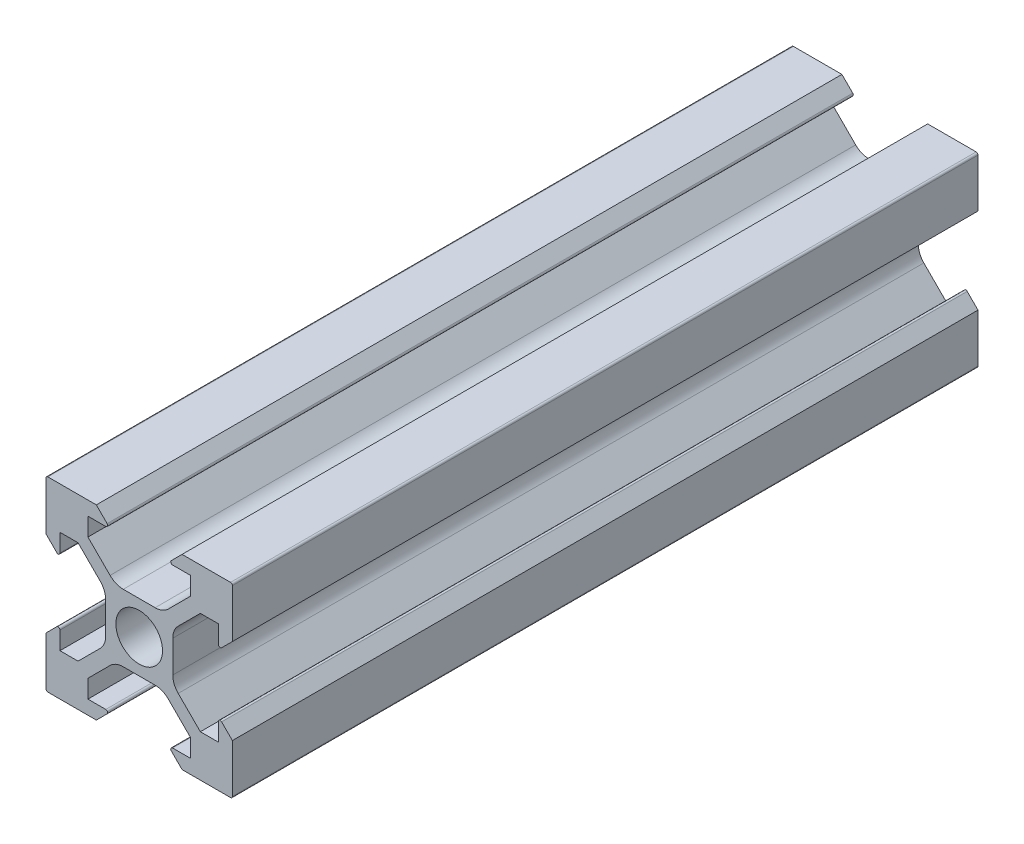
SolidWorks part; units mm, degrees
material "Liga 1350"
ref_plane "Plano frontal" through (0, 0, 0) normal (0, 0, 1) x (1, 0, 0)
ref_plane "Plano superior" through (0, 0, 0) normal (0, 1, 0) x (1, 0, 0)
ref_plane "Plano direito" through (0, 0, 0) normal (1, 0, 0) x (0, 0, -1)
sketch "Esboço1" plane through (0, 0, 0) normal (0, 0, 1) x (1, 0, 0)
  line L0 (0, 13.8681) -> (0, -15.879) construction
  line L1 (-4.6, -10) -> (-9.8, -10)
  line L2 (-3.4414, -8.8414) -> (-4.6, -10)
  line L3 (-4.1858, -3.1251) -> (-6.5607, -5.5)
  line L4 (-10, 9.8) -> (-10, 4.6)
  line L5 (-5.5, -8.5) -> (-3.5828, -8.5)
  line L6 (-5.5, -8.5) -> (-5.5, -6.5607)
  line L7 (-8.5, -5.5) -> (-8.5, -3.5828)
  line L8 (-21.5514, 0) -> (2.5, 0) construction
  line L9 (-3.1251, 4.1858) -> (-5.5, 6.5607)
  line L10 (-8.8414, -3.4414) -> (-10, -4.6)
  line L11 (-8.5, 5.5) -> (-6.5607, 5.5)
  line L12 (-8.8414, 3.4414) -> (-10, 4.6)
  line L13 (-8.5, -5.5) -> (-6.5607, -5.5)
  line L14 (-8.5, 5.5) -> (-8.5, 3.5828)
  line L15 (-3.1251, -4.1858) -> (-5.5, -6.5607)
  line L16 (-21.5514, 0) -> (20.6623, 0) construction
  line L17 (-8.5, 10) -> (-8.5, -10) construction
  line L18 (-10, -9.8) -> (-10, -4.6)
  line L19 (-21.5514, 5.5) -> (20.6623, 5.5) construction
  line L21 (-10, 10) -> (-10, -10) construction
  line L22 (3.6, 1.7109) -> (3.6, 0) construction
  line L23 (21.5514, 0) -> (-2.5, 0) construction
  line L24 (4.6, 10) -> (9.8, 10)
  line L25 (-5.5, 8.5) -> (-5.5, 6.5607)
  line L26 (3.4414, 8.8414) -> (4.6, 10)
  line L27 (-5.5, 8.5) -> (-3.5828, 8.5)
  line L28 (4.1858, 3.1251) -> (6.5607, 5.5)
  line L29 (5.5, 8.5) -> (3.5828, 8.5)
  line L30 (5.5, 8.5) -> (5.5, 6.5607)
  line L31 (-3.6, 1.7109) -> (-3.6, -1.7109)
  line L33 (10, -9.8) -> (10, -4.6)
  line L34 (-4.1858, 3.1251) -> (-6.5607, 5.5)
  line L35 (-3.4414, 8.8414) -> (-4.6, 10)
  line L36 (-4.6, 10) -> (-9.8, 10)
  line L37 (3.1251, -4.1858) -> (5.5, -6.5607)
  line L38 (8.5, 5.5) -> (8.5, 3.5828)
  line L39 (8.5, -5.5) -> (6.5607, -5.5)
  line L40 (8.8414, 3.4414) -> (10, 4.6)
  line L41 (8.5, 5.5) -> (6.5607, 5.5)
  line L42 (8.8414, -3.4414) -> (10, -4.6)
  line L43 (3.1251, 4.1858) -> (5.5, 6.5607)
  line L44 (8.5, -5.5) -> (8.5, -3.5828)
  line L45 (5.5, -8.5) -> (5.5, -6.5607)
  line L46 (5.5, -8.5) -> (3.5828, -8.5)
  line L47 (10, 9.8) -> (10, 4.6)
  line L48 (4.1858, -3.1251) -> (6.5607, -5.5)
  line L49 (3.4414, -8.8414) -> (4.6, -10)
  line L50 (4.6, -10) -> (9.8, -10)
  line L51 (-1.7109, 3.6) -> (1.7109, 3.6)
  line L52 (3.6, 1.7109) -> (3.6, -1.7109)
  line L53 (1.7109, -3.6) -> (-1.7109, -3.6)
  circle A0 centre (0, 0) radius 2.5
  arc A1 (-3.6, 1.7109) -> (-4.1858, 3.1251) centre (-5.6, 1.7109) ccw
  arc A2 (-8.5, 3.5828) -> (-8.8414, 3.4414) centre (-8.7, 3.5828) cw
  arc A3 (-9.8, 10) -> (-10, 9.8) centre (-9.8, 9.8) ccw
  arc A4 (-1.7109, 3.6) -> (-3.1251, 4.1858) centre (-1.7109, 5.6) cw
  arc A5 (-3.5828, 8.5) -> (-3.4414, 8.8414) centre (-3.5828, 8.7) ccw
  arc A6 (-3.5828, -8.5) -> (-3.4414, -8.8414) centre (-3.5828, -8.7) cw
  arc A7 (-1.7109, -3.6) -> (-3.1251, -4.1858) centre (-1.7109, -5.6) ccw
  arc A8 (-9.8, -10) -> (-10, -9.8) centre (-9.8, -9.8) cw
  arc A9 (-8.5, -3.5828) -> (-8.8414, -3.4414) centre (-8.7, -3.5828) ccw
  arc A10 (-3.6, -1.7109) -> (-4.1858, -3.1251) centre (-5.6, -1.7109) cw
  arc A11 (3.6, -1.7109) -> (4.1858, -3.1251) centre (5.6, -1.7109) ccw
  arc A12 (8.5, -3.5828) -> (8.8414, -3.4414) centre (8.7, -3.5828) cw
  arc A13 (9.8, -10) -> (10, -9.8) centre (9.8, -9.8) ccw
  arc A14 (1.7109, -3.6) -> (3.1251, -4.1858) centre (1.7109, -5.6) cw
  arc A15 (3.5828, -8.5) -> (3.4414, -8.8414) centre (3.5828, -8.7) ccw
  arc A16 (3.5828, 8.5) -> (3.4414, 8.8414) centre (3.5828, 8.7) cw
  arc A17 (1.7109, 3.6) -> (3.1251, 4.1858) centre (1.7109, 5.6) ccw
  arc A18 (9.8, 10) -> (10, 9.8) centre (9.8, 9.8) cw
  arc A19 (8.5, 3.5828) -> (8.8414, 3.4414) centre (8.7, 3.5828) ccw
  arc A20 (3.6, 1.7109) -> (4.1858, 3.1251) centre (5.6, 1.7109) cw
  point P0 (0, 0)
  point P45 (-3.6, 2.5393)
extrude "Ressalto-extrusão1" add sketch "Esboço1" along normal blind 80
